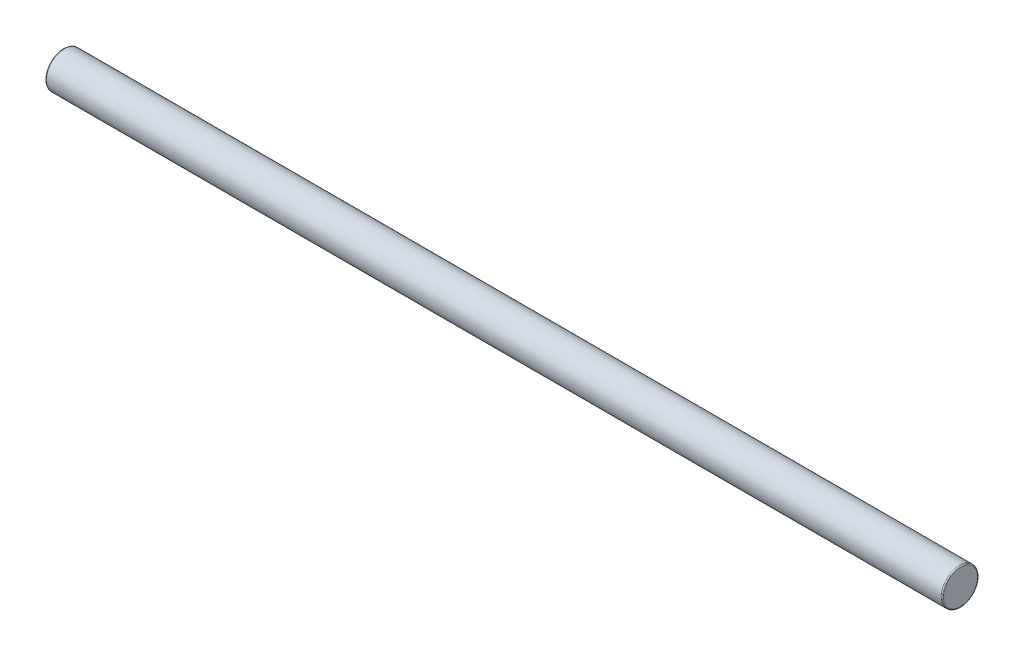
SolidWorks part; units mm, degrees
ref_plane "Front Plane" through (0, 0, 0) normal (0, 0, 1) x (1, 0, 0)
ref_plane "Top Plane" through (0, 0, 0) normal (0, 1, 0) x (1, 0, 0)
ref_plane "Right Plane" through (0, 0, 0) normal (1, 0, 0) x (0, 0, -1)
sketch "Sketch1" plane through (0, 0, 0) normal (1, 0, 0) x (0, 0, -1)
  circle A0 centre (0, 0) radius 0.381
  dimension "D1" = 0.762
extrude "Extrude1" add sketch "Sketch1" along normal blind 18.796
fillet "Fillet1" radius 0.0254 2 edges at (0, 0, -0.381) (18.796, 0, -0.381)
